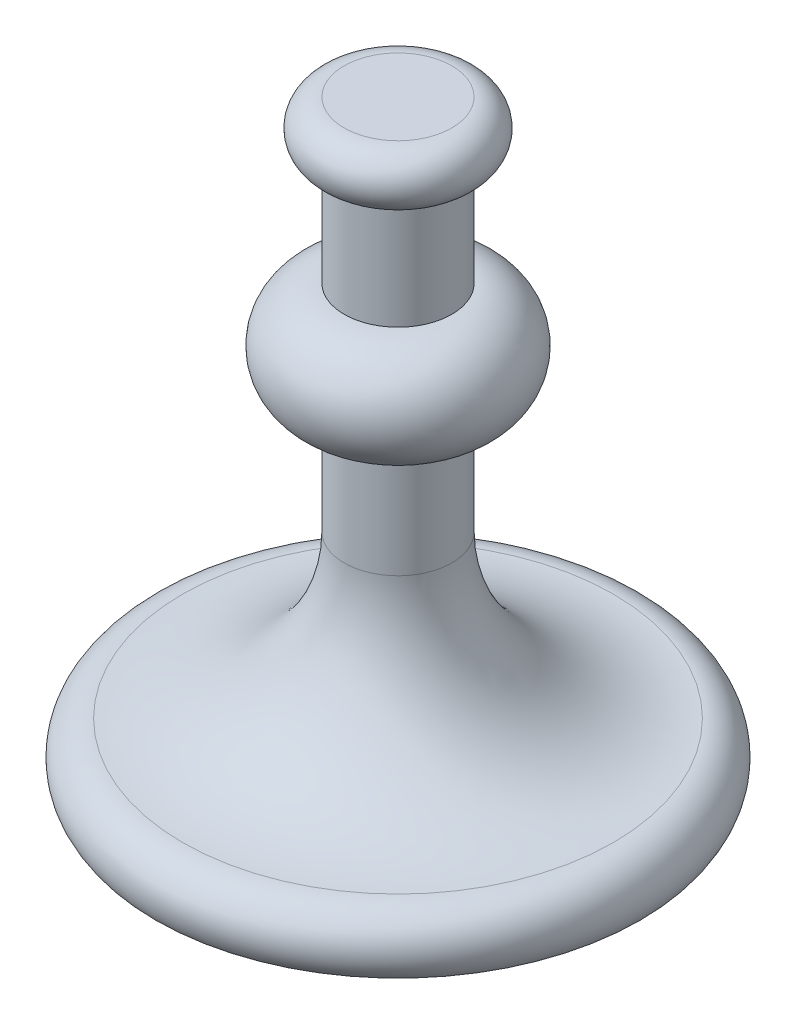
SolidWorks part; units mm, degrees
material "1060 Alloy"
ref_plane "Front Plane" through (0, 0, 0) normal (0, 0, 1) x (1, 0, 0)
ref_plane "Top Plane" through (0, 0, 0) normal (0, 1, 0) x (1, 0, 0)
ref_plane "Right Plane" through (0, 0, 0) normal (1, 0, 0) x (0, 0, -1)
sketch "Sketch2" plane through (0, 0, 0) normal (0, 0, 1) x (1, 0, 0)
  line L0 (0, 0) -> (0, 220)
  line L1 (0, 220) -> (20, 220)
  line L2 (20, 200) -> (20, 160)
  line L5 (0, 0) -> (90, 0)
  line L6 (20, 120) -> (20, 80)
  arc A0 (20, 220) -> (20, 200) centre (20, 210) cw
  arc A1 (20, 160) -> (20, 120) centre (20, 140) cw
  arc A4 (20, 80) -> (80, 20) centre (80, 80) ccw
  arc A5 (80, 20) -> (90, 0) centre (80, 7.5) cw
  dimension "D3" = 10
  dimension "D5" = 20
  dimension "D8" = 12.5
  dimension "D9" = 80
  dimension "D7" = 60
  dimension "D1" = 220
  dimension "D2" = 40
  dimension "D4" = 20
  dimension "D6" = 90
revolve "Revolve1" add sketch "Sketch2" angle 360 about L0
